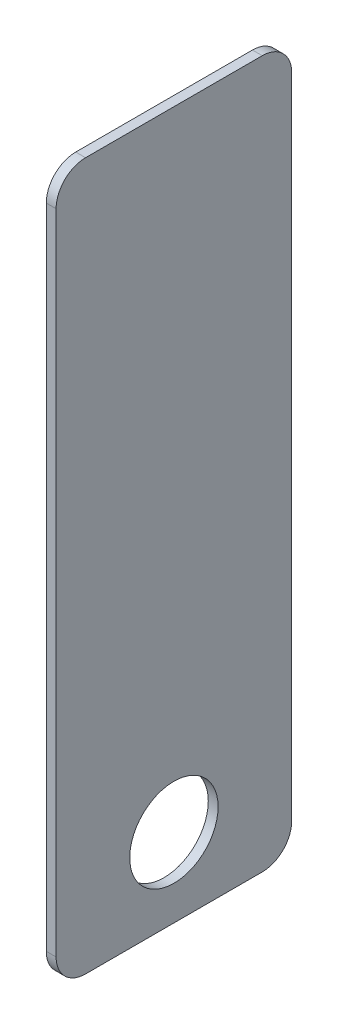
SolidWorks part; units mm, degrees
material "6063-O"
ref_plane "Front" through (0, 0, 0) normal (0, 0, 1) x (1, 0, 0)
ref_plane "Top" through (0, 0, 0) normal (0, 1, 0) x (1, 0, 0)
ref_plane "Right" through (0, 0, 0) normal (1, 0, 0) x (0, 0, -1)
sketch "Sketch1" plane through (0, 0, 0) normal (1, 0, 0) x (0, 0, -1)
  line L0 (0, 114.3) -> (0, -114.3) construction
  line L1 (-38.1, 114.3) -> (38.1, 114.3)
  line L2 (-38.1, 114.3) -> (-38.1, -114.3)
  line L3 (-38.1, -114.3) -> (38.1, -114.3)
  line L4 (38.1, 114.3) -> (38.1, -114.3)
  circle A0 centre (0, -88.9) radius 14.2875
  point P4 (0, 0)
  dimension "D3" = 28.575
  dimension "D1" = 76.2
  dimension "D2" = 203.2
  dimension "D4" = 25.4
extrude "Boss-Extrude1" add sketch "Sketch1" along normal blind 3.175
fillet "Fillet1" radius 9.525 4 edges at (1.5875, -114.3, -38.1) (1.5875, -114.3, 38.1) (1.5875, 114.3, -38.1) (1.5875, 114.3, 38.1)
